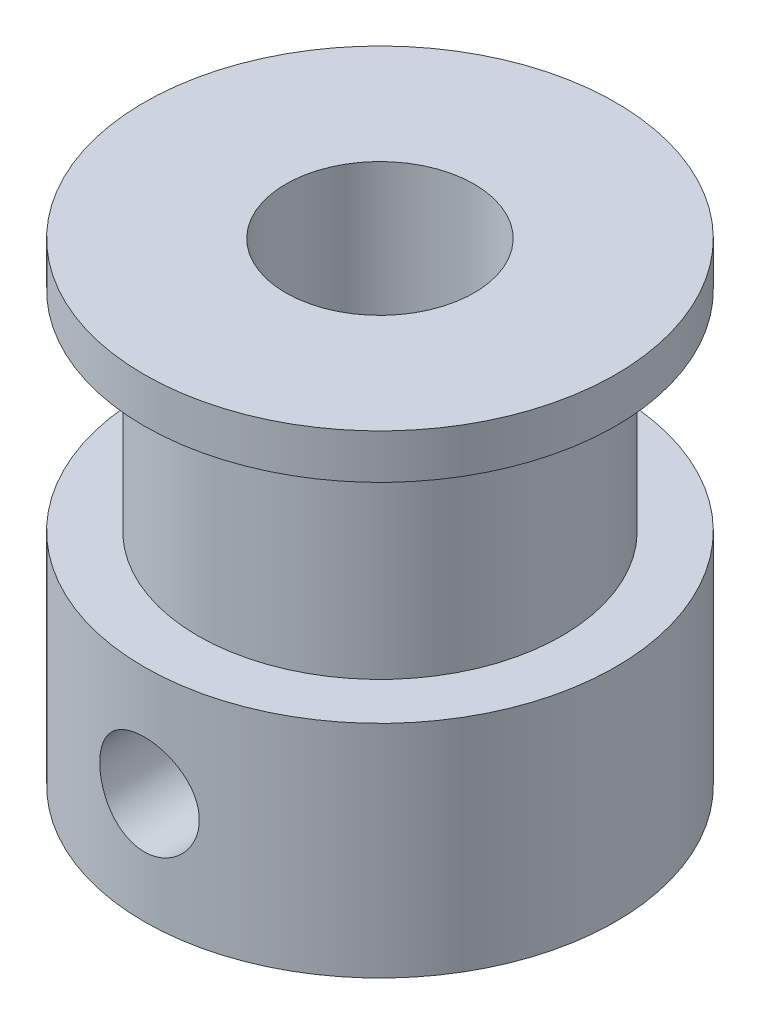
SolidWorks part; units mm, degrees
ref_plane "Front Plane" through (0, 0, 0) normal (0, 0, 1) x (1, 0, 0)
ref_plane "Top Plane" through (0, 0, 0) normal (0, 1, 0) x (1, 0, 0)
ref_plane "Right Plane" through (0, 0, 0) normal (1, 0, 0) x (0, 0, -1)
sketch "Sketch1" plane through (0, 0, 0) normal (0, 1, 0) x (1, 0, 0)
  circle A0 centre (0, 0) radius 3.17
  circle A1 centre (0, 0) radius 7.93
  dimension "D1" = 15.86
  dimension "D2" = 6.34
extrude "Boss-Extrude1" add sketch "Sketch1" along normal blind 7.42
sketch "Sketch2" plane through (0, 7.42, 0) normal (0, 1, 0) x (1, 0, 0)
  circle A0 centre (0, 0) radius 6.12
  circle A1 centre (0, 0) radius 3.17
  dimension "D1" = 12.24
extrude "Boss-Extrude2" add sketch "Sketch2" along normal blind 7.02 contours A0 | A1
sketch "Sketch3" plane through (0, 14.44, 0) normal (0, 1, 0) x (1, 0, 0)
  circle A0 centre (0, 0) radius 3.17
  circle A1 centre (0, 0) radius 7.93
extrude "Boss-Extrude3" add sketch "Sketch3" along normal blind 1.5
sketch "Sketch4" plane through (0, 0, 0) normal (1, 0, 0) x (0, 0, -1)
  line L0 (0, 7.42) -> (0, 0) construction
  line L1 (7.93, 7.42) -> (-7.93, 7.42) construction
  circle A0 centre (0, 3.71) radius 1.675
  dimension "D1" = 3.35
extrude "Cut-Extrude1" cut sketch "Sketch4" against normal through all
pattern_circular "CirPattern1" count 2 every 90 about axis through (0, 7.42, 0) along (0, -1, 0) of "Cut-Extrude1"
